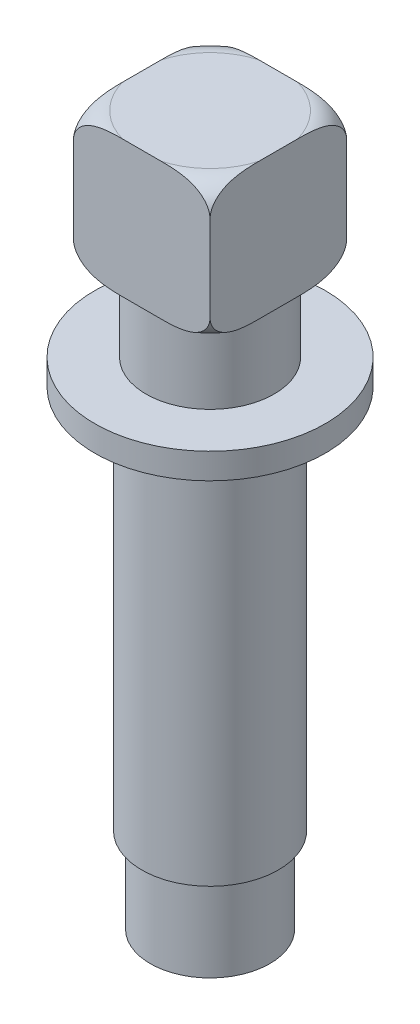
SolidWorks part; units mm, degrees
ref_plane "Front Plane" through (0, 0, 0) normal (0, 0, 1) x (1, 0, 0)
ref_plane "Top Plane" through (0, 0, 0) normal (0, 1, 0) x (1, 0, 0)
ref_plane "Right Plane" through (0, 0, 0) normal (1, 0, 0) x (0, 0, -1)
sketch "Sketch1" plane through (0, 0, 0) normal (0, 0, 1) x (1, 0, 0)
  line L0 (0, 0) -> (7, 0)
  line L1 (7, 0) -> (7, 10)
  line L2 (7, 10) -> (8, 10)
  line L3 (8, 10) -> (8, 55)
  line L4 (8, 55) -> (13.5, 55)
  line L5 (13.5, 55) -> (13.5, 58)
  line L6 (13.5, 58) -> (7.5, 58)
  line L7 (7.5, 58) -> (7.5, 67)
  line L8 (7.5, 67) -> (0, 67)
  line L9 (0, 0) -> (0, 71.1124) construction
  line L10 (0, 0) -> (0, 67)
  dimension "D1" = 7
  dimension "D2" = 10
  dimension "D3" = 8
  dimension "D4" = 45
  dimension "D5" = 3
  dimension "D6" = 13.5
  dimension "D7" = 7.5
  dimension "D8" = 9
revolve "Revolve1" add sketch "Sketch1" angle 360 about L9
sketch "Sketch2" plane through (0, 67, 0) normal (0, 1, 0) x (1, 0, 0)
  line L1 (-8, 8) -> (8, 8)
  line L2 (-8, 8) -> (-8, -8)
  line L3 (-8, -8) -> (8, -8)
  line L4 (8, 8) -> (8, -8)
  line L5 (0, -8) -> (0, 8) construction
  line L6 (-8, 0) -> (8, 0) construction
  point P0 (0, 0)
  dimension "D1" = 16
  dimension "D2" = 16
extrude "Boss-Extrude1" add sketch "Sketch2" along normal blind 16
ref_plane "Plane1" through (0, 0, 0) normal (0.7071, 0, 0.7071) x (0.7071, 0, -0.7071)
sketch "Sketch4" plane through (0, 0, 0) normal (0.7071, 0, 0.7071) x (0.7071, 0, -0.7071)
  line L0 (11.3137, 83) -> (8.3137, 83)
  line L2 (11.3137, 80) -> (11.3137, 83)
  line L3 (11.3137, 83) -> (11.3137, 67) construction
  line L4 (0, 66.5288) -> (0, 68.9912) construction
  line L5 (0, 83) -> (0, 67) construction
  line L6 (11.3137, 67) -> (8.3137, 67)
  line L7 (0, 67) -> (11.3137, 67) construction
  line L8 (11.3137, 70) -> (11.3137, 67)
  arc A0 (11.3137, 80) -> (8.3137, 83) centre (8.3137, 80) ccw
  arc A1 (11.3137, 70) -> (8.3137, 67) centre (8.3137, 70) cw
  point P2 (0, 0)
  point P10 (11.3137, 83)
  point P17 (7.1901, 67)
  point P19 (11.3137, 72.0625)
  point P22 (11.3137, 67)
  point P23 (11.3137, 67)
  point P24 (11.0267, 67)
  dimension "D1" = 3
  dimension "D2" = 3
revolve "Cut-Revolve1" cut sketch "Sketch4" angle 360 about L4
